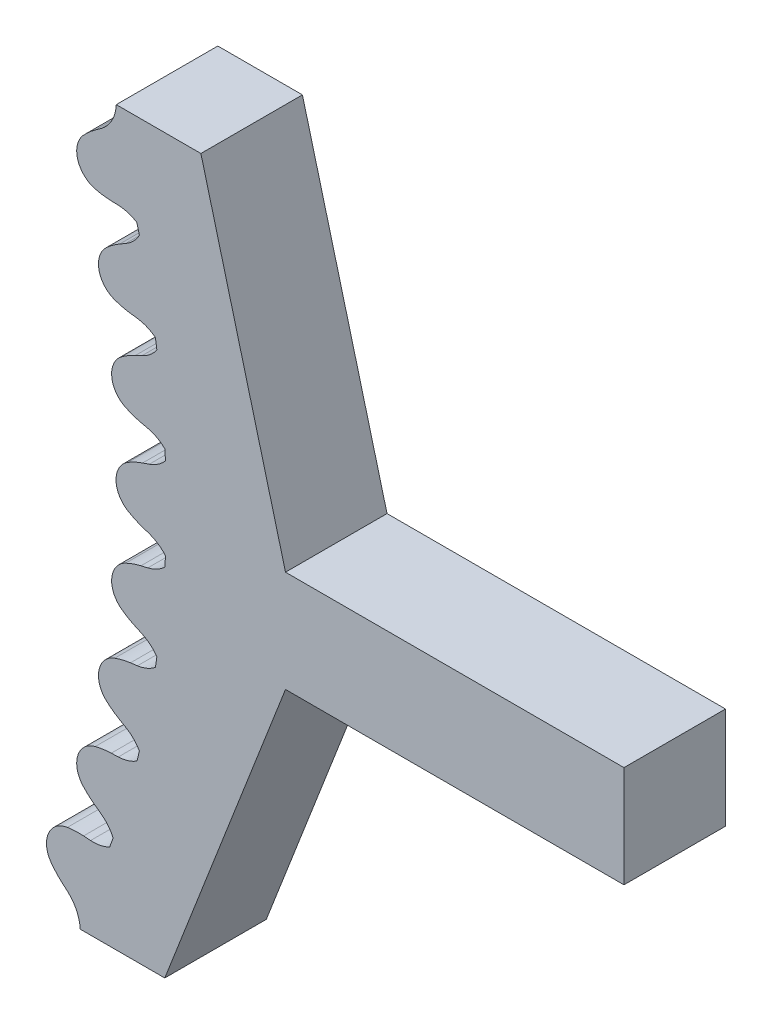
SolidWorks part; units mm, degrees
ref_plane "Front Plane" through (0, 0, 0) normal (0, 0, 1) x (1, 0, 0)
ref_plane "Top Plane" through (0, 0, 0) normal (0, 1, 0) x (1, 0, 0)
ref_plane "Right Plane" through (0, 0, 0) normal (1, 0, 0) x (0, 0, -1)
sketch "Sketch1" plane through (0, 0, 0) normal (0, 0, 1) x (1, 0, 0)
  line L1 (73.0847, 24.3892) -> (79.4347, 0.3512)
  line L2 (79.4347, -7.2688) -> (70.3743, -30.5528)
  line L4 (64.0243, -30.5528) -> (70.3743, -30.5528)
  line L5 (66.7347, 24.3892) -> (73.0847, 24.3892)
  line L6 (79.4347, 0.3512) -> (104.8347, 0.3512)
  line L7 (79.4347, -3.4588) -> (104.8347, -3.4588) construction
  line L8 (79.4347, -7.2688) -> (104.8347, -7.2688)
  line L9 (104.8347, 0.3512) -> (104.8347, -7.2688)
  line L19 (63.0798, -28.5737) -> (62.683, -28.2249)
  line L20 (64.2816, -24.3655) -> (64.8088, -24.3995)
  line L21 (65.5768, -22.2532) -> (65.1477, -21.945)
  line L22 (66.3603, -17.9475) -> (66.8883, -17.9297)
  line L23 (67.4422, -15.7184) -> (66.985, -15.4537)
  line L24 (67.8, -11.3566) -> (68.3236, -11.2871)
  line L25 (68.6581, -9.0322) -> (68.1772, -8.8137)
  line L26 (68.5866, -4.6564) -> (69.101, -4.5359)
  line L28 (65.1477, 21.945) -> (65.5768, 22.2532)
  line L29 (66.8883, 17.9297) -> (66.3603, 17.9475)
  line L30 (66.985, 15.4537) -> (67.4422, 15.7184)
  line L31 (69.2128, -2.259) -> (68.7128, -2.0887)
  line L32 (68.7128, 2.0887) -> (69.2128, 2.259)
  line L33 (69.101, 4.5359) -> (68.5866, 4.6564)
  line L34 (68.1772, 8.8137) -> (68.6581, 9.0322)
  line L35 (68.3236, 11.2871) -> (67.8, 11.3566)
  arc A77 (64.0243, -30.5528) -> (63.0798, -28.5737) centre (61.2405, -30.6664) ccw
  arc A78 (61.5694, -26.7428) -> (61.8597, -27.3303) centre (63.3368, -26.235) ccw
  arc A79 (61.8597, -27.3303) -> (62.683, -28.2249) centre (66.4816, -23.903) ccw
  arc A81 (62.4462, -24.6261) -> (61.5694, -26.7428) centre (63.3368, -26.235) ccw
  arc A82 (63.0669, -24.416) -> (62.4462, -24.6261) centre (63.3368, -26.235) ccw
  arc A83 (64.2816, -24.3655) -> (63.0669, -24.416) centre (63.9116, -30.1076) ccw
  arc A84 (64.8088, -24.3995) -> (66.2403, -24.108) centre (64.988, -21.6192) ccw
  arc A85 (66.2403, -24.108) -> (66.4984, -23.3867) centre (0, 0) ccw
  arc A86 (66.4984, -23.3867) -> (65.5768, -22.2532) centre (63.9515, -24.5161) ccw
  arc A87 (64.2407, -21.1354) -> (65.1477, -21.945) centre (68.5043, -17.2716) ccw
  arc A88 (63.8942, -20.5792) -> (64.2407, -21.1354) centre (65.6033, -19.9006) ccw
  arc A89 (64.5593, -18.3867) -> (63.8942, -20.5792) centre (65.6033, -19.9006) ccw
  arc A90 (65.1564, -18.1168) -> (64.5593, -18.3867) centre (65.6033, -19.9006) ccw
  arc A91 (66.3603, -17.9475) -> (65.1564, -18.1168) centre (66.5549, -23.6982) ccw
  arc A92 (66.8883, -17.9297) -> (68.2844, -17.4992) centre (66.7941, -15.1452) ccw
  arc A93 (68.2844, -17.4992) -> (68.4705, -16.7561) centre (0, 0) ccw
  arc A94 (68.4705, -16.7561) -> (67.4422, -15.7184) centre (66.0465, -18.1297) ccw
  arc A95 (66.003, -14.7369) -> (66.985, -15.4537) centre (69.8674, -10.4738) ccw
  arc A96 (65.6037, -14.2174) -> (66.003, -14.7369) centre (67.238, -13.3745) ccw
  arc A97 (66.6184, -11.6431) -> (66.0506, -11.9703) centre (67.238, -13.3745) ccw
  arc A98 (66.0506, -11.9703) -> (65.6037, -14.2174) centre (67.238, -13.3745) ccw
  arc A99 (67.8, -11.3566) -> (66.6184, -11.6431) centre (68.5572, -17.0605) ccw
  arc A100 (68.3236, -11.2871) -> (69.6708, -10.7219) centre (67.957, -8.5253) ccw
  arc A101 (69.6708, -10.7219) -> (69.7832, -9.9642) centre (0, 0) ccw
  arc A102 (69.7832, -9.9642) -> (68.6581, -9.0322) centre (67.5055, -11.5687) ccw
  arc A103 (67.1296, -8.1966) -> (68.1772, -8.8137) centre (70.5576, -3.5752) ccw
  arc A104 (66.6813, -7.7186) -> (67.1296, -8.1966) centre (68.2252, -6.7196) ccw
  arc A105 (66.9059, -5.4385) -> (66.6813, -7.7186) centre (68.2252, -6.7196) ccw
  arc A106 (67.4388, -5.0573) -> (66.9059, -5.4385) centre (68.2252, -6.7196) ccw
  arc A107 (68.5866, -4.6564) -> (67.4388, -5.0573) centre (69.8993, -10.2586) ccw
  arc A108 (69.101, -4.5359) -> (70.3862, -3.8413) centre (68.4653, -1.8233) ccw
  arc A109 (70.3862, -3.8413) -> (70.4238, -3.0762) centre (0, 0) ccw
  arc A115 (65.5768, 22.2532) -> (66.7347, 24.3892) centre (63.9515, 24.5161) ccw
  arc A116 (65.1477, 21.945) -> (64.2407, 21.1354) centre (68.5043, 17.2716) ccw
  arc A117 (64.2407, 21.1354) -> (63.8942, 20.5792) centre (65.6033, 19.9006) ccw
  arc A118 (63.8942, 20.5792) -> (64.5593, 18.3867) centre (65.6033, 19.9006) ccw
  arc A119 (64.5593, 18.3867) -> (65.1564, 18.1168) centre (65.6033, 19.9006) ccw
  arc A120 (65.1564, 18.1168) -> (66.3603, 17.9475) centre (66.5549, 23.6982) ccw
  arc A121 (68.2844, 17.4992) -> (66.8883, 17.9297) centre (66.7941, 15.1452) ccw
  arc A122 (68.4705, 16.7561) -> (68.2844, 17.4992) centre (0, 0) ccw
  arc A123 (67.4422, 15.7184) -> (68.4705, 16.7561) centre (66.0465, 18.1297) ccw
  arc A124 (66.985, 15.4537) -> (66.003, 14.7369) centre (69.8674, 10.4738) ccw
  arc A125 (66.003, 14.7369) -> (65.6037, 14.2174) centre (67.238, 13.3745) ccw
  arc A126 (65.6037, 14.2174) -> (66.0506, 11.9703) centre (67.238, 13.3745) ccw
  arc A127 (70.4238, -3.0762) -> (69.2128, -2.259) centre (68.3144, -4.8963) ccw
  arc A128 (67.6098, -1.5772) -> (68.7128, -2.0887) centre (70.5683, 3.3579) ccw
  arc A129 (67.1168, -1.1456) -> (67.6098, -1.5772) centre (68.5553, 0) ccw
  arc A130 (67.1168, 1.1456) -> (67.1168, -1.1456) centre (68.5553, 0) ccw
  arc A131 (67.6098, 1.5772) -> (67.1168, 1.1456) centre (68.5553, 0) ccw
  arc A132 (68.7128, 2.0887) -> (67.6098, 1.5772) centre (70.5683, -3.3579) ccw
  arc A133 (69.2128, 2.259) -> (70.4238, 3.0762) centre (68.3144, 4.8963) ccw
  arc A134 (70.4238, 3.0762) -> (70.3862, 3.8413) centre (0, 0) ccw
  arc A135 (70.3862, 3.8413) -> (69.101, 4.5359) centre (68.4653, 1.8233) ccw
  arc A136 (67.4388, 5.0573) -> (68.5866, 4.6564) centre (69.8993, 10.2586) ccw
  arc A137 (66.9059, 5.4385) -> (67.4388, 5.0573) centre (68.2252, 6.7196) ccw
  arc A138 (66.6813, 7.7186) -> (66.9059, 5.4385) centre (68.2252, 6.7196) ccw
  arc A139 (66.0506, 11.9703) -> (66.6184, 11.6431) centre (67.238, 13.3745) ccw
  arc A140 (67.1296, 8.1966) -> (66.6813, 7.7186) centre (68.2252, 6.7196) ccw
  arc A141 (68.1772, 8.8137) -> (67.1296, 8.1966) centre (70.5576, 3.5752) ccw
  arc A142 (68.6581, 9.0322) -> (69.7832, 9.9642) centre (67.5055, 11.5687) ccw
  arc A143 (69.7832, 9.9642) -> (69.6708, 10.7219) centre (0, 0) ccw
  arc A144 (69.6708, 10.7219) -> (68.3236, 11.2871) centre (67.957, 8.5253) ccw
  arc A145 (66.6184, 11.6431) -> (67.8, 11.3566) centre (68.5572, 17.0605) ccw
  point P2 (70.4061, -3.4588)
  point P4 (0, 0)
  point P7 (0, 0)
  dimension "D1" = 6.35
  dimension "D2" = 6.35
  dimension "D3" = 3.81
  dimension "D4" = 3.81
  dimension "D5" = 25.4
  dimension "D6" = 3.81
  dimension "D7" = 3.81
extrude "Boss-Extrude1" add sketch "Sketch1" along normal blind 7.62
